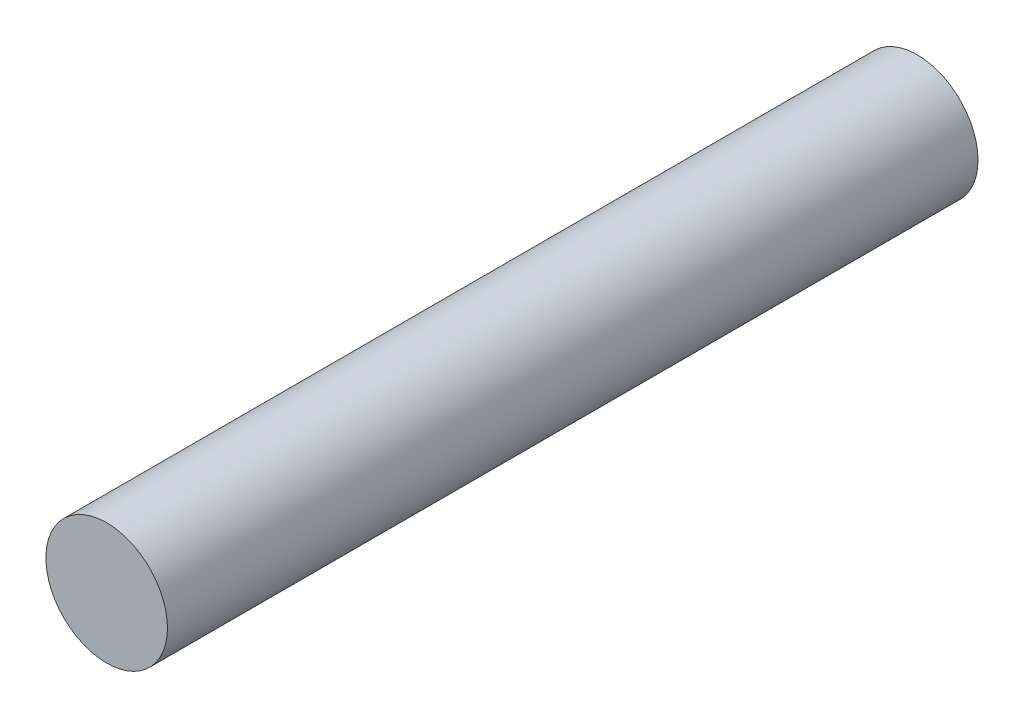
SolidWorks part; units mm, degrees
ref_plane "Front Plane" through (0, 0, 0) normal (0, 0, 1) x (1, 0, 0)
ref_plane "Top Plane" through (0, 0, 0) normal (0, 1, 0) x (1, 0, 0)
ref_plane "Right Plane" through (0, 0, 0) normal (1, 0, 0) x (0, 0, -1)
sketch "Sketch1" plane through (0, 0, 0) normal (0, 0, 1) x (1, 0, 0)
  circle A0 centre (0, 0) radius 19.05
  dimension "D1" = 38.1
extrude "Boss-Extrude1" add sketch "Sketch1" along normal blind 254
equation "\"Valve Hole\"= 1.5"
equation "\"D1@Sketch1\"=\"Valve Hole\""
equation "\"duck\" = 5"
